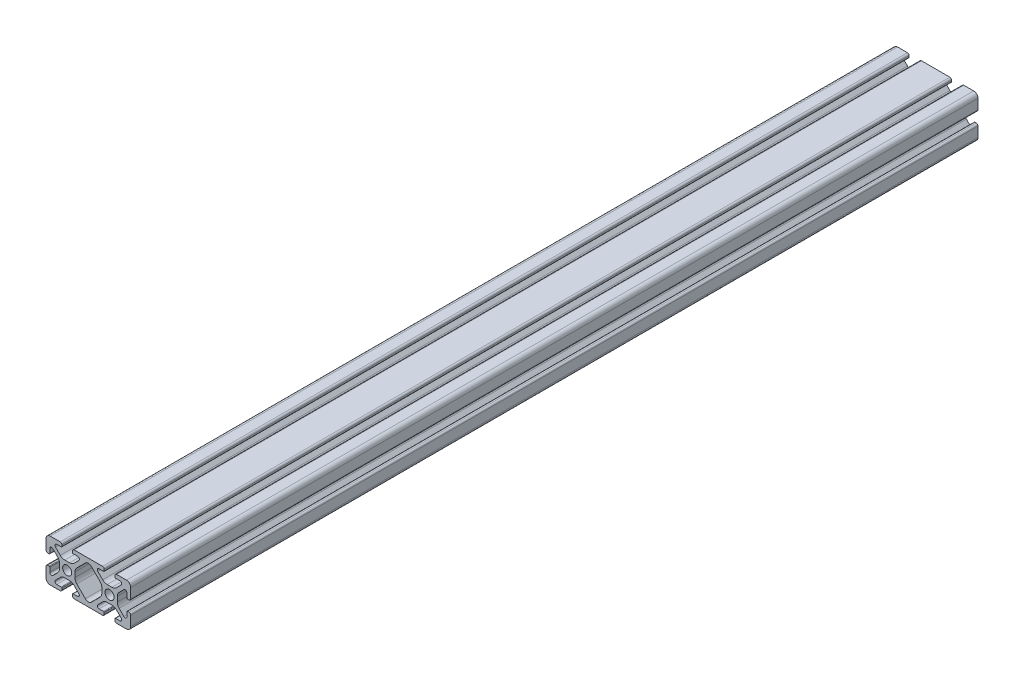
SolidWorks part; units mm, degrees
ref_plane "Alzado" through (0, 0, 0) normal (0, 0, 1) x (1, 0, 0)
ref_plane "Planta" through (0, 0, 0) normal (0, 1, 0) x (1, 0, 0)
ref_plane "Vista lateral" through (0, 0, 0) normal (1, 0, 0) x (0, 0, -1)
ref_plane "Plano1" through (0, 0, 20) normal (0, 0, 1) x (1, 0, 0)
sketch "Croquis1" plane through (0, 0, 20) normal (0, 0, 1) x (1, 0, 0)
  line L0 (32.5, 1.5) -> (32.5, 0.8)
  line L1 (33.3, 0) -> (38, 0)
  line L2 (40, 2) -> (40, 6.7)
  line L3 (39.2, 7.5) -> (38.5, 7.5)
  line L4 (38.2, 7.2) -> (38.2, 5.0824)
  line L5 (36.779, 4.4938) -> (34.5287, 6.7441)
  line L6 (33.65, 8.8654) -> (33.65, 11.1346)
  line L7 (34.5287, 13.2559) -> (36.779, 15.5062)
  line L8 (38.2, 14.9176) -> (38.2, 12.8)
  line L9 (38.5, 12.5) -> (39.2, 12.5)
  line L10 (40, 13.3) -> (40, 18)
  line L11 (38, 20) -> (33.3, 20)
  line L12 (32.5, 19.2) -> (32.5, 18.5)
  line L13 (32.8, 18.2) -> (34.9176, 18.2)
  line L14 (35.5062, 16.779) -> (33.2559, 14.5287)
  line L15 (31.1346, 13.65) -> (28.8654, 13.65)
  line L16 (26.7441, 14.5287) -> (24.4938, 16.779)
  line L17 (25.0824, 18.2) -> (27.2, 18.2)
  line L18 (27.5, 18.5) -> (27.5, 19.2)
  line L19 (26.7, 20) -> (13.3, 20)
  line L20 (12.5, 19.2) -> (12.5, 18.5)
  line L21 (12.8, 18.2) -> (14.9176, 18.2)
  line L22 (15.5062, 16.779) -> (13.2559, 14.5287)
  line L23 (11.1346, 13.65) -> (8.8654, 13.65)
  line L24 (6.7441, 14.5287) -> (4.4938, 16.779)
  line L25 (5.0824, 18.2) -> (7.2, 18.2)
  line L26 (7.5, 18.5) -> (7.5, 19.2)
  line L27 (6.7, 20) -> (2, 20)
  line L28 (0, 18) -> (0, 13.3)
  line L29 (0.8, 12.5) -> (1.5, 12.5)
  line L30 (1.8, 12.8) -> (1.8, 14.9176)
  line L31 (3.221, 15.5062) -> (5.4713, 13.2559)
  line L32 (6.35, 11.1346) -> (6.35, 8.8654)
  line L33 (5.4713, 6.7441) -> (3.221, 4.4938)
  line L34 (1.8, 5.0824) -> (1.8, 7.2)
  line L35 (1.5, 7.5) -> (0.8, 7.5)
  line L36 (0, 6.7) -> (0, 2)
  line L37 (2, 0) -> (6.7, 0)
  line L38 (7.5, 0.8) -> (7.5, 1.5)
  line L39 (7.2, 1.8) -> (5.0824, 1.8)
  line L40 (4.4938, 3.221) -> (6.7441, 5.4713)
  line L41 (8.8654, 6.35) -> (11.1346, 6.35)
  line L42 (13.2559, 5.4713) -> (15.5062, 3.221)
  line L43 (14.9176, 1.8) -> (12.8, 1.8)
  line L44 (12.5, 1.5) -> (12.5, 0.8)
  line L45 (13.3, 0) -> (26.7, 0)
  line L46 (27.5, 0.8) -> (27.5, 1.5)
  line L47 (27.2, 1.8) -> (25.0824, 1.8)
  line L48 (24.4938, 3.221) -> (26.7441, 5.4713)
  line L49 (28.8654, 6.35) -> (31.1346, 6.35)
  line L50 (33.2559, 5.4713) -> (35.5062, 3.221)
  line L51 (34.9176, 1.8) -> (32.8, 1.8)
  line L52 (18.5858, 2.687) -> (14.5287, 6.7441)
  line L53 (13.65, 8.8654) -> (13.65, 11.1346)
  line L54 (14.5287, 13.2559) -> (18.5858, 17.313)
  line L55 (21.4142, 17.313) -> (25.4713, 13.2559)
  line L56 (26.35, 11.1346) -> (26.35, 8.8654)
  line L57 (25.4713, 6.7441) -> (21.4142, 2.687)
  arc A0 (32.8, 1.8) -> (32.5, 1.5) centre (32.8, 1.5) ccw
  arc A1 (32.5, 0.8) -> (33.3, 0) centre (33.3, 0.8) ccw
  arc A2 (38, 0) -> (40, 2) centre (38, 2) ccw
  arc A3 (40, 6.7) -> (39.2, 7.5) centre (39.2, 6.7) ccw
  arc A4 (38.5, 7.5) -> (38.2, 7.2) centre (38.5, 7.2) ccw
  arc A5 (38.2, 5.0824) -> (36.779, 4.4938) centre (37.3676, 5.0824) cw
  arc A6 (34.5287, 6.7441) -> (33.65, 8.8654) centre (36.65, 8.8654) cw
  arc A7 (33.65, 11.1346) -> (34.5287, 13.2559) centre (36.65, 11.1346) cw
  arc A8 (36.779, 15.5062) -> (38.2, 14.9176) centre (37.3676, 14.9176) cw
  arc A9 (38.2, 12.8) -> (38.5, 12.5) centre (38.5, 12.8) ccw
  arc A10 (39.2, 12.5) -> (40, 13.3) centre (39.2, 13.3) ccw
  arc A11 (40, 18) -> (38, 20) centre (38, 18) ccw
  arc A12 (33.3, 20) -> (32.5, 19.2) centre (33.3, 19.2) ccw
  arc A13 (32.5, 18.5) -> (32.8, 18.2) centre (32.8, 18.5) ccw
  arc A14 (34.9176, 18.2) -> (35.5062, 16.779) centre (34.9176, 17.3676) cw
  arc A15 (33.2559, 14.5287) -> (31.1346, 13.65) centre (31.1346, 16.65) cw
  arc A16 (28.8654, 13.65) -> (26.7441, 14.5287) centre (28.8654, 16.65) cw
  arc A17 (24.4938, 16.779) -> (25.0824, 18.2) centre (25.0824, 17.3676) cw
  arc A18 (27.2, 18.2) -> (27.5, 18.5) centre (27.2, 18.5) ccw
  arc A19 (27.5, 19.2) -> (26.7, 20) centre (26.7, 19.2) ccw
  arc A20 (13.3, 20) -> (12.5, 19.2) centre (13.3, 19.2) ccw
  arc A21 (12.5, 18.5) -> (12.8, 18.2) centre (12.8, 18.5) ccw
  arc A22 (14.9176, 18.2) -> (15.5062, 16.779) centre (14.9176, 17.3676) cw
  arc A23 (13.2559, 14.5287) -> (11.1346, 13.65) centre (11.1346, 16.65) cw
  arc A24 (8.8654, 13.65) -> (6.7441, 14.5287) centre (8.8654, 16.65) cw
  arc A25 (4.4938, 16.779) -> (5.0824, 18.2) centre (5.0824, 17.3676) cw
  arc A26 (7.2, 18.2) -> (7.5, 18.5) centre (7.2, 18.5) ccw
  arc A27 (7.5, 19.2) -> (6.7, 20) centre (6.7, 19.2) ccw
  arc A28 (2, 20) -> (0, 18) centre (2, 18) ccw
  arc A29 (0, 13.3) -> (0.8, 12.5) centre (0.8, 13.3) ccw
  arc A30 (1.5, 12.5) -> (1.8, 12.8) centre (1.5, 12.8) ccw
  arc A31 (1.8, 14.9176) -> (3.221, 15.5062) centre (2.6324, 14.9176) cw
  arc A32 (5.4713, 13.2559) -> (6.35, 11.1346) centre (3.35, 11.1346) cw
  arc A33 (6.35, 8.8654) -> (5.4713, 6.7441) centre (3.35, 8.8654) cw
  arc A34 (3.221, 4.4938) -> (1.8, 5.0824) centre (2.6324, 5.0824) cw
  arc A35 (1.8, 7.2) -> (1.5, 7.5) centre (1.5, 7.2) ccw
  arc A36 (0.8, 7.5) -> (0, 6.7) centre (0.8, 6.7) ccw
  arc A37 (0, 2) -> (2, 0) centre (2, 2) ccw
  arc A38 (6.7, 0) -> (7.5, 0.8) centre (6.7, 0.8) ccw
  arc A39 (7.5, 1.5) -> (7.2, 1.8) centre (7.2, 1.5) ccw
  arc A40 (5.0824, 1.8) -> (4.4938, 3.221) centre (5.0824, 2.6324) cw
  arc A41 (6.7441, 5.4713) -> (8.8654, 6.35) centre (8.8654, 3.35) cw
  arc A42 (11.1346, 6.35) -> (13.2559, 5.4713) centre (11.1346, 3.35) cw
  arc A43 (15.5062, 3.221) -> (14.9176, 1.8) centre (14.9176, 2.6324) cw
  arc A44 (12.8, 1.8) -> (12.5, 1.5) centre (12.8, 1.5) ccw
  arc A45 (12.5, 0.8) -> (13.3, 0) centre (13.3, 0.8) ccw
  arc A46 (26.7, 0) -> (27.5, 0.8) centre (26.7, 0.8) ccw
  arc A47 (27.5, 1.5) -> (27.2, 1.8) centre (27.2, 1.5) ccw
  arc A48 (25.0824, 1.8) -> (24.4938, 3.221) centre (25.0824, 2.6324) cw
  arc A49 (26.7441, 5.4713) -> (28.8654, 6.35) centre (28.8654, 3.35) cw
  arc A50 (31.1346, 6.35) -> (33.2559, 5.4713) centre (31.1346, 3.35) cw
  arc A51 (35.5062, 3.221) -> (34.9176, 1.8) centre (34.9176, 2.6324) cw
  circle A52 centre (10, 10) radius 2.15
  circle A53 centre (30, 10) radius 2.15
  arc A54 (21.4142, 2.687) -> (18.5858, 2.687) centre (20, 4.1012) cw
  arc A55 (14.5287, 6.7441) -> (13.65, 8.8654) centre (16.65, 8.8654) cw
  arc A56 (13.65, 11.1346) -> (14.5287, 13.2559) centre (16.65, 11.1346) cw
  arc A57 (18.5858, 17.313) -> (21.4142, 17.313) centre (20, 15.8988) cw
  arc A58 (25.4713, 13.2559) -> (26.35, 11.1346) centre (23.35, 11.1346) cw
  arc A59 (26.35, 8.8654) -> (25.4713, 6.7441) centre (23.35, 8.8654) cw
extrude "Saliente-Extruir1" add sketch "Croquis1" against normal blind 400
